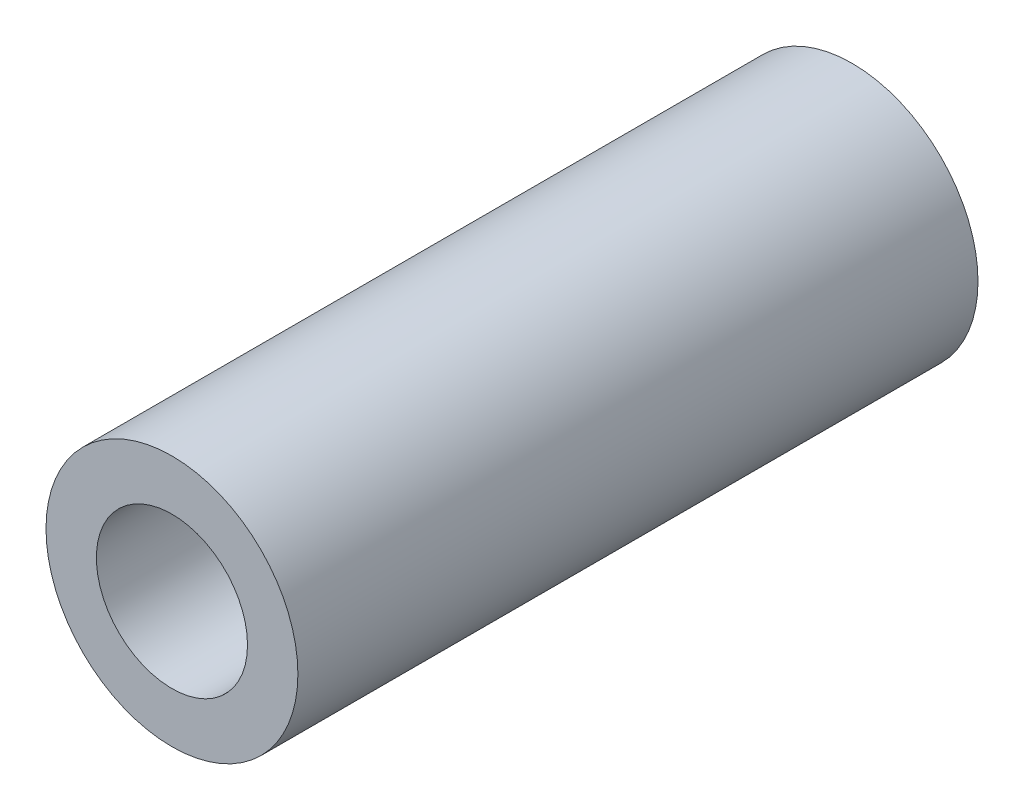
SolidWorks part; units mm, degrees
ref_plane "Plano frontal" through (0, 0, 0) normal (0, 0, 1) x (1, 0, 0)
ref_plane "Plano superior" through (0, 0, 0) normal (0, 1, 0) x (1, 0, 0)
ref_plane "Plano direito" through (0, 0, 0) normal (1, 0, 0) x (0, 0, -1)
sketch "Esboço1" plane through (0, 0, 0) normal (0, 0, 1) x (1, 0, 0)
  circle A0 centre (0, 0) radius 3
  circle A1 centre (0, 0) radius 5
  dimension "D1" = 6
  dimension "D2" = 10
extrude "Ressalto-extrusão1" add sketch "Esboço1" along normal blind 27 contours A1
